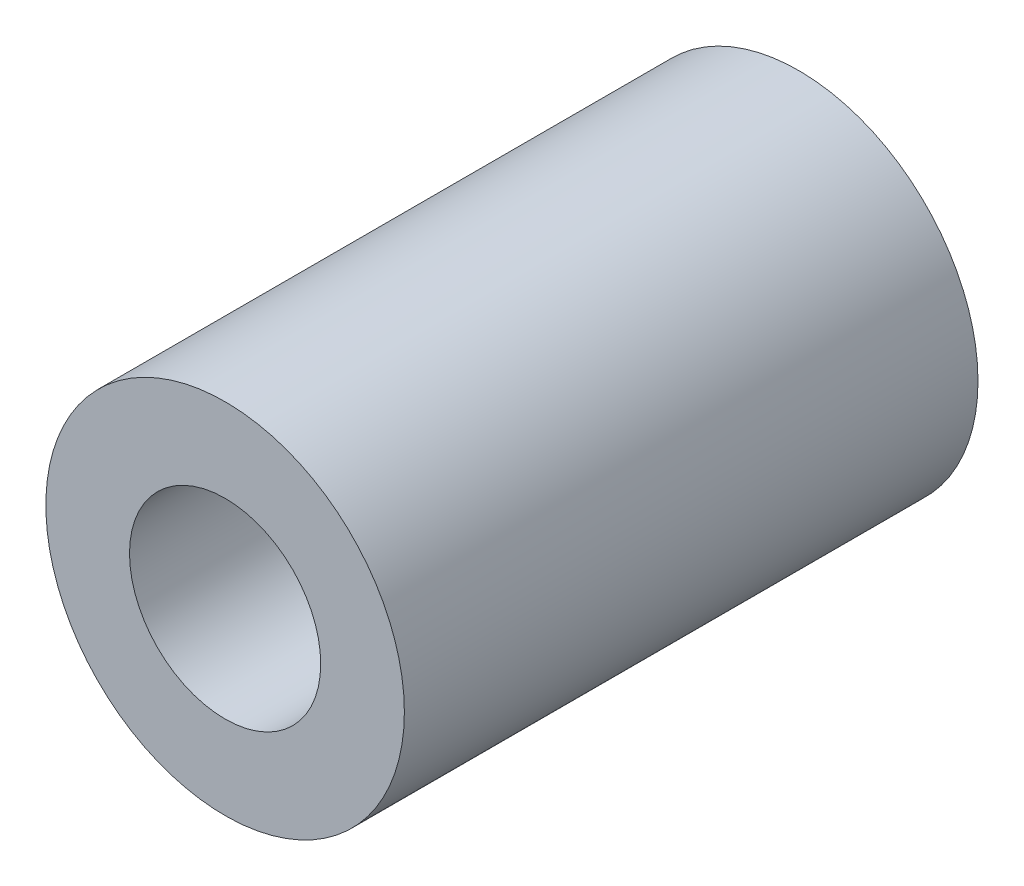
SolidWorks part; units mm, degrees
ref_plane "前视基准面" through (0, 0, 0) normal (0, 0, 1) x (1, 0, 0)
ref_plane "上视基准面" through (0, 0, 0) normal (0, 1, 0) x (1, 0, 0)
ref_plane "右视基准面" through (0, 0, 0) normal (1, 0, 0) x (0, 0, -1)
sketch "草图1" plane through (0, 0, 0) normal (0, 0, 1) x (1, 0, 0)
  circle A0 centre (0, 0) radius 7.5
  circle A1 centre (0, 0) radius 4
  dimension "D1" = 8
  dimension "D2" = 15
extrude "凸台-拉伸1" add sketch "草图1" along normal mid plane 24
